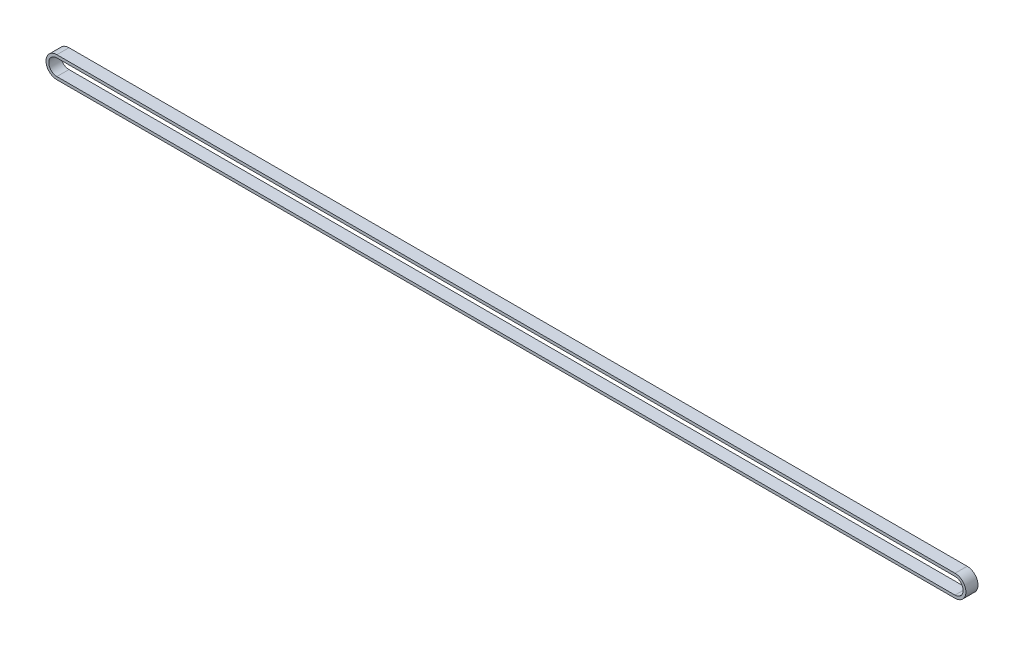
SolidWorks part; units mm, degrees
ref_plane "Front Plane" through (0, 0, 0) normal (0, 0, 1) x (1, 0, 0)
ref_plane "Top Plane" through (0, 0, 0) normal (0, 1, 0) x (1, 0, 0)
ref_plane "Right Plane" through (0, 0, 0) normal (1, 0, 0) x (0, 0, -1)
sketch "Sketch1" plane through (0, 0, 0) normal (0, 0, 1) x (1, 0, 0)
  line L0 (-222.5, 5.38) -> (222.5, 5.38)
  line L1 (-222.5, -4) -> (222.5, -4)
  line L3 (-222.5, 4) -> (222.5, 4)
  line L5 (-222.5, -4) -> (222.5, 4) construction
  line L6 (-222.5, 4) -> (222.5, -4) construction
  line L7 (-222.5, -5.38) -> (222.5, -5.38)
  arc A0 (-222.5, 4) -> (-222.5, -4) centre (-222.5, 0) ccw
  arc A1 (222.5, -4) -> (222.5, 4) centre (222.5, 0) ccw
  arc A2 (222.5, -5.38) -> (222.5, 5.38) centre (222.5, 0) ccw
  arc A3 (-222.5, 5.38) -> (-222.5, -5.38) centre (-222.5, 0) ccw
  point P0 (0, 0)
  dimension "D1" = 4
  dimension "D2" = 445
  dimension "D3" = 1.38
extrude "Boss-Extrude1" add sketch "Sketch1" along normal blind 6
